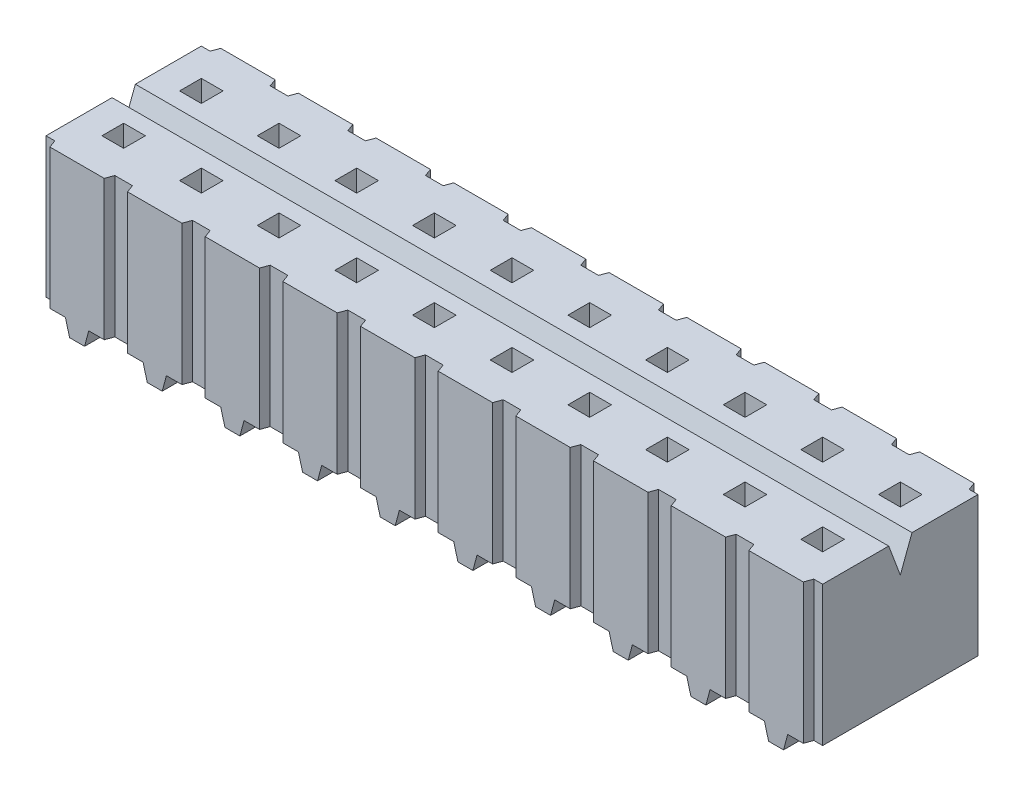
SolidWorks part; units mm, degrees
material "CA"
ref_plane "Front Plane" through (0, 0, 0) normal (0, 0, 1) x (1, 0, 0)
ref_plane "Top Plane" through (0, 0, 0) normal (0, 1, 0) x (1, 0, 0)
ref_plane "Right Plane" through (0, 0, 0) normal (1, 0, 0) x (0, 0, -1)
ref_plane "Plane1" through (0, 0.508, 0) normal (0, -1, 0) x (1, 0, 0)
sketch "Sketch1" plane through (0, 0.508, 0) normal (0, -1, 0) x (1, 0, 0)
  line L0 (-12.319, -2.794) -> (-10.541, -2.794)
  line L1 (-10.541, -2.794) -> (-10.541, -2.54)
  line L2 (-10.541, -2.54) -> (-9.779, -2.54)
  line L3 (-9.779, -2.54) -> (-9.779, -2.794)
  line L4 (-9.779, -2.794) -> (-8.001, -2.794)
  line L5 (-8.001, -2.794) -> (-8.001, -2.54)
  line L6 (-8.001, -2.54) -> (-7.239, -2.54)
  line L7 (-7.239, -2.54) -> (-7.239, -2.794)
  line L8 (-7.239, -2.794) -> (-5.461, -2.794)
  line L9 (-5.461, -2.794) -> (-5.461, -2.54)
  line L10 (-5.461, -2.54) -> (-4.699, -2.54)
  line L11 (-4.699, -2.54) -> (-4.699, -2.794)
  line L12 (-4.699, -2.794) -> (-2.921, -2.794)
  line L13 (-2.921, -2.794) -> (-2.921, -2.54)
  line L14 (-2.921, -2.54) -> (-2.159, -2.54)
  line L15 (-2.159, -2.54) -> (-2.159, -2.794)
  line L16 (-2.159, -2.794) -> (-0.381, -2.794)
  line L17 (-0.381, -2.794) -> (-0.381, -2.54)
  line L18 (-0.381, -2.54) -> (0.381, -2.54)
  line L19 (0.381, -2.54) -> (0.381, -2.794)
  line L20 (0.381, -2.794) -> (2.159, -2.794)
  line L21 (2.159, -2.794) -> (2.159, -2.54)
  line L22 (2.159, -2.54) -> (2.921, -2.54)
  line L23 (2.921, -2.54) -> (2.921, -2.794)
  line L24 (2.921, -2.794) -> (4.699, -2.794)
  line L25 (4.699, -2.794) -> (4.699, -2.54)
  line L26 (4.699, -2.54) -> (5.461, -2.54)
  line L27 (5.461, -2.54) -> (5.461, -2.794)
  line L28 (5.461, -2.794) -> (7.239, -2.794)
  line L29 (7.239, -2.794) -> (7.239, -2.54)
  line L30 (7.239, -2.54) -> (8.001, -2.54)
  line L31 (8.001, -2.54) -> (8.001, -2.794)
  line L32 (8.001, -2.794) -> (9.779, -2.794)
  line L33 (9.779, -2.794) -> (9.779, -2.54)
  line L34 (9.779, -2.54) -> (10.541, -2.54)
  line L35 (10.541, -2.54) -> (10.541, -2.794)
  line L36 (10.541, -2.794) -> (12.319, -2.794)
  line L37 (12.319, -2.794) -> (12.319, -2.54)
  line L38 (12.319, -2.54) -> (12.7, -2.54)
  line L39 (12.7, -2.54) -> (12.7, 2.54)
  line L40 (12.7, 2.54) -> (12.319, 2.54)
  line L41 (12.319, 2.54) -> (12.319, 2.794)
  line L42 (12.319, 2.794) -> (10.541, 2.794)
  line L43 (10.541, 2.794) -> (10.541, 2.54)
  line L44 (10.541, 2.54) -> (9.779, 2.54)
  line L45 (9.779, 2.54) -> (9.779, 2.794)
  line L46 (9.779, 2.794) -> (8.001, 2.794)
  line L47 (8.001, 2.794) -> (8.001, 2.54)
  line L48 (8.001, 2.54) -> (7.239, 2.54)
  line L49 (7.239, 2.54) -> (7.239, 2.794)
  line L50 (7.239, 2.794) -> (5.461, 2.794)
  line L51 (5.461, 2.794) -> (5.461, 2.54)
  line L52 (5.461, 2.54) -> (4.699, 2.54)
  line L53 (4.699, 2.54) -> (4.699, 2.794)
  line L54 (4.699, 2.794) -> (2.921, 2.794)
  line L55 (2.921, 2.794) -> (2.921, 2.54)
  line L56 (2.921, 2.54) -> (2.159, 2.54)
  line L57 (2.159, 2.54) -> (2.159, 2.794)
  line L58 (2.159, 2.794) -> (0.381, 2.794)
  line L59 (0.381, 2.794) -> (0.381, 2.54)
  line L60 (0.381, 2.54) -> (-0.381, 2.54)
  line L61 (-0.381, 2.54) -> (-0.381, 2.794)
  line L62 (-0.381, 2.794) -> (-2.159, 2.794)
  line L63 (-2.159, 2.794) -> (-2.159, 2.54)
  line L64 (-2.159, 2.54) -> (-2.921, 2.54)
  line L65 (-2.921, 2.54) -> (-2.921, 2.794)
  line L66 (-2.921, 2.794) -> (-4.699, 2.794)
  line L67 (-4.699, 2.794) -> (-4.699, 2.54)
  line L68 (-4.699, 2.54) -> (-5.461, 2.54)
  line L69 (-5.461, 2.54) -> (-5.461, 2.794)
  line L70 (-5.461, 2.794) -> (-7.239, 2.794)
  line L71 (-7.239, 2.794) -> (-7.239, 2.54)
  line L72 (-7.239, 2.54) -> (-8.001, 2.54)
  line L73 (-8.001, 2.54) -> (-8.001, 2.794)
  line L74 (-8.001, 2.794) -> (-9.779, 2.794)
  line L75 (-9.779, 2.794) -> (-9.779, 2.54)
  line L76 (-9.779, 2.54) -> (-10.541, 2.54)
  line L77 (-10.541, 2.54) -> (-10.541, 2.794)
  line L78 (-10.541, 2.794) -> (-12.319, 2.794)
  line L79 (-12.319, 2.794) -> (-12.319, 2.54)
  line L80 (-12.319, 2.54) -> (-12.7, 2.54)
  line L81 (-12.7, 2.54) -> (-12.7, -2.54)
  line L82 (-12.7, -2.54) -> (-12.319, -2.54)
  line L83 (-12.319, -2.54) -> (-12.319, -2.794)
extrude "Boss-Extrude1" add sketch "Sketch1" against normal blind 4.572
draft "Draft1" type of draft neutral plane draft angle 20 faces to draft 2 face at (-12.319, 2.794, -2.667) face at (-10.541, 2.794, -2.667) neutral plane through (-12.319, 5.08, -2.794) neutral plane normal (0, 0, -1) parameters "D1"=20
draft "Draft2" type of draft neutral plane draft angle 20 faces to draft 2 face at (-9.779, 2.794, -2.667) face at (-8.001, 2.794, -2.667) neutral plane through (-9.779, 5.08, -2.794) neutral plane normal (0, 0, -1) parameters "D1"=20
draft "Draft3" type of draft neutral plane draft angle 20 faces to draft 2 face at (-7.239, 2.794, -2.667) face at (-5.461, 2.794, -2.667) neutral plane through (-7.239, 5.08, -2.794) neutral plane normal (0, 0, -1) parameters "D1"=20
draft "Draft4" type of draft neutral plane draft angle 20 faces to draft 2 face at (-4.699, 2.794, -2.667) face at (-2.921, 2.794, -2.667) neutral plane through (-4.699, 5.08, -2.794) neutral plane normal (0, 0, -1) parameters "D1"=20
draft "Draft5" type of draft neutral plane draft angle 20 faces to draft 2 face at (-2.159, 2.794, -2.667) face at (-0.381, 2.794, -2.667) neutral plane through (-2.159, 5.08, -2.794) neutral plane normal (0, 0, -1) parameters "D1"=20
draft "Draft6" type of draft neutral plane draft angle 20 faces to draft 2 face at (0.381, 2.794, -2.667) face at (2.159, 2.794, -2.667) neutral plane through (0.381, 5.08, -2.794) neutral plane normal (0, 0, -1) parameters "D1"=20
draft "Draft7" type of draft neutral plane draft angle 20 faces to draft 2 face at (2.921, 2.794, -2.667) face at (4.699, 2.794, -2.667) neutral plane through (2.921, 5.08, -2.794) neutral plane normal (0, 0, -1) parameters "D1"=20
draft "Draft8" type of draft neutral plane draft angle 20 faces to draft 2 face at (5.461, 2.794, -2.667) face at (7.239, 2.794, -2.667) neutral plane through (5.461, 5.08, -2.794) neutral plane normal (0, 0, -1) parameters "D1"=20
draft "Draft9" type of draft neutral plane draft angle 20 faces to draft 2 face at (8.001, 2.794, -2.667) face at (9.779, 2.794, -2.667) neutral plane through (8.001, 5.08, -2.794) neutral plane normal (0, 0, -1) parameters "D1"=20
draft "Draft10" type of draft neutral plane draft angle 20 faces to draft 2 face at (10.541, 2.794, -2.667) face at (12.319, 2.794, -2.667) neutral plane through (10.541, 5.08, -2.794) neutral plane normal (0, 0, -1) parameters "D1"=20
draft "Draft11" type of draft neutral plane draft angle 20 faces to draft 2 face at (-10.541, 2.794, 2.667) face at (-12.319, 2.794, 2.667) neutral plane through (-10.541, 5.08, 2.794) neutral plane normal (0, 0, 1) parameters "D1"=20
draft "Draft12" type of draft neutral plane draft angle 20 faces to draft 2 face at (-8.001, 2.794, 2.667) face at (-9.779, 2.794, 2.667) neutral plane through (-8.001, 5.08, 2.794) neutral plane normal (0, 0, 1) parameters "D1"=20
draft "Draft13" type of draft neutral plane draft angle 20 faces to draft 2 face at (-5.461, 2.794, 2.667) face at (-7.239, 2.794, 2.667) neutral plane through (-5.461, 5.08, 2.794) neutral plane normal (0, 0, 1) parameters "D1"=20
draft "Draft14" type of draft neutral plane draft angle 20 faces to draft 2 face at (-2.921, 2.794, 2.667) face at (-4.699, 2.794, 2.667) neutral plane through (-2.921, 5.08, 2.794) neutral plane normal (0, 0, 1) parameters "D1"=20
draft "Draft15" type of draft neutral plane draft angle 20 faces to draft 2 face at (-0.381, 2.794, 2.667) face at (-2.159, 2.794, 2.667) neutral plane through (-0.381, 5.08, 2.794) neutral plane normal (0, 0, 1) parameters "D1"=20
draft "Draft16" type of draft neutral plane draft angle 20 faces to draft 2 face at (2.159, 2.794, 2.667) face at (0.381, 2.794, 2.667) neutral plane through (2.159, 5.08, 2.794) neutral plane normal (0, 0, 1) parameters "D1"=20
draft "Draft17" type of draft neutral plane draft angle 20 faces to draft 2 face at (4.699, 2.794, 2.667) face at (2.921, 2.794, 2.667) neutral plane through (4.699, 5.08, 2.794) neutral plane normal (0, 0, 1) parameters "D1"=20
draft "Draft18" type of draft neutral plane draft angle 20 faces to draft 2 face at (7.239, 2.794, 2.667) face at (5.461, 2.794, 2.667) neutral plane through (7.239, 5.08, 2.794) neutral plane normal (0, 0, 1) parameters "D1"=20
draft "Draft19" type of draft neutral plane draft angle 20 faces to draft 2 face at (9.779, 2.794, 2.667) face at (8.001, 2.794, 2.667) neutral plane through (9.779, 5.08, 2.794) neutral plane normal (0, 0, 1) parameters "D1"=20
draft "Draft20" type of draft neutral plane draft angle 20 faces to draft 2 face at (10.541, 2.794, 2.667) face at (12.319, 2.794, 2.667) neutral plane through (12.319, 5.08, 2.794) neutral plane normal (0, 0, 1) parameters "D1"=20
sketch "Sketch2" plane through (0, 0.508, 0) normal (0, -1, 0) x (1, 0, 0)
  line L0 (-11.049, -2.794) -> (-11.811, -2.794)
  line L1 (-11.811, -2.794) -> (-11.811, -2.286)
  line L2 (-11.811, -2.286) -> (-11.049, -2.286)
  line L3 (-11.049, -2.286) -> (-11.049, -2.794)
extrude "Boss-Extrude2" add sketch "Sketch2" along normal blind 0.508
sketch "Sketch3" plane through (0, 0.508, 0) normal (0, -1, 0) x (1, 0, 0)
  line L0 (-9.271, -2.286) -> (-8.509, -2.286)
  line L1 (-8.509, -2.286) -> (-8.509, -2.794)
  line L2 (-8.509, -2.794) -> (-9.271, -2.794)
  line L3 (-9.271, -2.794) -> (-9.271, -2.286)
extrude "Boss-Extrude3" add sketch "Sketch3" along normal blind 0.508
sketch "Sketch4" plane through (0, 0.508, 0) normal (0, -1, 0) x (1, 0, 0)
  line L0 (-6.731, -2.286) -> (-5.969, -2.286)
  line L1 (-5.969, -2.286) -> (-5.969, -2.794)
  line L2 (-5.969, -2.794) -> (-6.731, -2.794)
  line L3 (-6.731, -2.794) -> (-6.731, -2.286)
extrude "Boss-Extrude4" add sketch "Sketch4" along normal blind 0.508
sketch "Sketch5" plane through (0, 0.508, 0) normal (0, -1, 0) x (1, 0, 0)
  line L0 (-4.191, -2.286) -> (-3.429, -2.286)
  line L1 (-3.429, -2.286) -> (-3.429, -2.794)
  line L2 (-3.429, -2.794) -> (-4.191, -2.794)
  line L3 (-4.191, -2.794) -> (-4.191, -2.286)
extrude "Boss-Extrude5" add sketch "Sketch5" along normal blind 0.508
sketch "Sketch6" plane through (0, 0.508, 0) normal (0, -1, 0) x (1, 0, 0)
  line L0 (-1.651, -2.286) -> (-0.889, -2.286)
  line L1 (-0.889, -2.286) -> (-0.889, -2.794)
  line L2 (-0.889, -2.794) -> (-1.651, -2.794)
  line L3 (-1.651, -2.794) -> (-1.651, -2.286)
extrude "Boss-Extrude6" add sketch "Sketch6" along normal blind 0.508
sketch "Sketch7" plane through (0, 0.508, 0) normal (0, -1, 0) x (1, 0, 0)
  line L0 (0.889, -2.286) -> (1.651, -2.286)
  line L1 (1.651, -2.286) -> (1.651, -2.794)
  line L2 (1.651, -2.794) -> (0.889, -2.794)
  line L3 (0.889, -2.794) -> (0.889, -2.286)
extrude "Boss-Extrude7" add sketch "Sketch7" along normal blind 0.508
sketch "Sketch8" plane through (0, 0.508, 0) normal (0, -1, 0) x (1, 0, 0)
  line L0 (3.429, -2.286) -> (4.191, -2.286)
  line L1 (4.191, -2.286) -> (4.191, -2.794)
  line L2 (4.191, -2.794) -> (3.429, -2.794)
  line L3 (3.429, -2.794) -> (3.429, -2.286)
extrude "Boss-Extrude8" add sketch "Sketch8" along normal blind 0.508
sketch "Sketch9" plane through (0, 0.508, 0) normal (0, -1, 0) x (1, 0, 0)
  line L0 (5.969, -2.286) -> (6.731, -2.286)
  line L1 (6.731, -2.286) -> (6.731, -2.794)
  line L2 (6.731, -2.794) -> (5.969, -2.794)
  line L3 (5.969, -2.794) -> (5.969, -2.286)
extrude "Boss-Extrude9" add sketch "Sketch9" along normal blind 0.508
sketch "Sketch10" plane through (0, 0.508, 0) normal (0, -1, 0) x (1, 0, 0)
  line L0 (8.509, -2.286) -> (9.271, -2.286)
  line L1 (9.271, -2.286) -> (9.271, -2.794)
  line L2 (9.271, -2.794) -> (8.509, -2.794)
  line L3 (8.509, -2.794) -> (8.509, -2.286)
extrude "Boss-Extrude10" add sketch "Sketch10" along normal blind 0.508
sketch "Sketch11" plane through (0, 0.508, 0) normal (0, -1, 0) x (1, 0, 0)
  line L0 (8.509, 2.794) -> (9.271, 2.794)
  line L1 (9.271, 2.794) -> (9.271, 2.286)
  line L2 (9.271, 2.286) -> (8.509, 2.286)
  line L3 (8.509, 2.286) -> (8.509, 2.794)
extrude "Boss-Extrude11" add sketch "Sketch11" along normal blind 0.508
sketch "Sketch12" plane through (0, 0.508, 0) normal (0, -1, 0) x (1, 0, 0)
  line L0 (5.969, 2.794) -> (6.731, 2.794)
  line L1 (6.731, 2.794) -> (6.731, 2.286)
  line L2 (6.731, 2.286) -> (5.969, 2.286)
  line L3 (5.969, 2.286) -> (5.969, 2.794)
extrude "Boss-Extrude12" add sketch "Sketch12" along normal blind 0.508
sketch "Sketch13" plane through (0, 0.508, 0) normal (0, -1, 0) x (1, 0, 0)
  line L0 (3.429, 2.794) -> (4.191, 2.794)
  line L1 (4.191, 2.794) -> (4.191, 2.286)
  line L2 (4.191, 2.286) -> (3.429, 2.286)
  line L3 (3.429, 2.286) -> (3.429, 2.794)
extrude "Boss-Extrude13" add sketch "Sketch13" along normal blind 0.508
sketch "Sketch14" plane through (0, 0.508, 0) normal (0, -1, 0) x (1, 0, 0)
  line L0 (0.889, 2.794) -> (1.651, 2.794)
  line L1 (1.651, 2.794) -> (1.651, 2.286)
  line L2 (1.651, 2.286) -> (0.889, 2.286)
  line L3 (0.889, 2.286) -> (0.889, 2.794)
extrude "Boss-Extrude14" add sketch "Sketch14" along normal blind 0.508
sketch "Sketch15" plane through (0, 0.508, 0) normal (0, -1, 0) x (1, 0, 0)
  line L0 (-1.651, 2.794) -> (-0.889, 2.794)
  line L1 (-0.889, 2.794) -> (-0.889, 2.286)
  line L2 (-0.889, 2.286) -> (-1.651, 2.286)
  line L3 (-1.651, 2.286) -> (-1.651, 2.794)
extrude "Boss-Extrude15" add sketch "Sketch15" along normal blind 0.508
sketch "Sketch16" plane through (0, 0.508, 0) normal (0, -1, 0) x (1, 0, 0)
  line L0 (-4.191, 2.794) -> (-3.429, 2.794)
  line L1 (-3.429, 2.794) -> (-3.429, 2.286)
  line L2 (-3.429, 2.286) -> (-4.191, 2.286)
  line L3 (-4.191, 2.286) -> (-4.191, 2.794)
extrude "Boss-Extrude16" add sketch "Sketch16" along normal blind 0.508
sketch "Sketch17" plane through (0, 0.508, 0) normal (0, -1, 0) x (1, 0, 0)
  line L0 (-6.731, 2.794) -> (-5.969, 2.794)
  line L1 (-5.969, 2.794) -> (-5.969, 2.286)
  line L2 (-5.969, 2.286) -> (-6.731, 2.286)
  line L3 (-6.731, 2.286) -> (-6.731, 2.794)
extrude "Boss-Extrude17" add sketch "Sketch17" along normal blind 0.508
sketch "Sketch18" plane through (0, 0.508, 0) normal (0, -1, 0) x (1, 0, 0)
  line L0 (-9.271, 2.794) -> (-8.509, 2.794)
  line L1 (-8.509, 2.794) -> (-8.509, 2.286)
  line L2 (-8.509, 2.286) -> (-9.271, 2.286)
  line L3 (-9.271, 2.286) -> (-9.271, 2.794)
extrude "Boss-Extrude18" add sketch "Sketch18" along normal blind 0.508
sketch "Sketch19" plane through (0, 0.508, 0) normal (0, -1, 0) x (1, 0, 0)
  line L0 (-11.049, 2.286) -> (-11.811, 2.286)
  line L1 (-11.811, 2.286) -> (-11.811, 2.794)
  line L2 (-11.811, 2.794) -> (-11.049, 2.794)
  line L3 (-11.049, 2.794) -> (-11.049, 2.286)
extrude "Boss-Extrude19" add sketch "Sketch19" along normal blind 0.508
sketch "Sketch20" plane through (0, 0.508, 0) normal (0, -1, 0) x (1, 0, 0)
  line L0 (11.049, 2.794) -> (11.811, 2.794)
  line L1 (11.811, 2.794) -> (11.811, 2.286)
  line L2 (11.811, 2.286) -> (11.049, 2.286)
  line L3 (11.049, 2.286) -> (11.049, 2.794)
extrude "Boss-Extrude20" add sketch "Sketch20" along normal blind 0.508
sketch "Sketch21" plane through (0, 0.508, 0) normal (0, -1, 0) x (1, 0, 0)
  line L0 (11.049, -2.286) -> (11.811, -2.286)
  line L1 (11.811, -2.286) -> (11.811, -2.794)
  line L2 (11.811, -2.794) -> (11.049, -2.794)
  line L3 (11.049, -2.794) -> (11.049, -2.286)
extrude "Boss-Extrude21" add sketch "Sketch21" along normal blind 0.508
draft "Draft21" type of draft neutral plane draft angle 15 faces to draft 40 face at (-11.049, 0.254, 2.54) face at (-8.509, 0.254, 2.54) face at (-5.969, 0.254, 2.54) face at (-3.429, 0.254, 2.54) face at (-0.889, 0.254, 2.54) face at (1.651, 0.254, 2.54) face at (4.191, 0.254, 2.54) face at (-11.049, 0.254, -2.54) face at (-8.509, 0.254, -2.54) face at (-5.969, 0.254, -2.54) face at (-3.429, 0.254, -2.54) face at (-0.889, 0.254, -2.54) face at (1.651, 0.254, -2.54) face at (4.191, 0.254, -2.54) face at (6.731, 0.254, 2.54) face at (6.731, 0.254, -2.54) face at (9.271, 0.254, 2.54) face at (9.271, 0.254, -2.54) face at (11.811, 0.254, 2.54) face at (11.811, 0.254, -2.54) face at (-9.271, 0.254, 2.54) face at (-6.731, 0.254, 2.54) face at (-4.191, 0.254, 2.54) face at (-1.651, 0.254, 2.54) face at (0.889, 0.254, 2.54) face at (3.429, 0.254, 2.54) face at (5.969, 0.254, 2.54) face at (8.509, 0.254, 2.54) face at (11.049, 0.254, 2.54) face at (11.049, 0.254, -2.54) face at (8.509, 0.254, -2.54) face at (5.969, 0.254, -2.54) face at (3.429, 0.254, -2.54) face at (0.889, 0.254, -2.54) face at (-1.651, 0.254, -2.54) face at (-4.191, 0.254, -2.54) face at (-6.731, 0.254, -2.54) face at (-9.271, 0.254, -2.54) face at (-11.811, 0.254, -2.54) face at (-11.811, 0.254, 2.54) neutral plane through (0, 0.508, 0) neutral plane normal (0, -1, 0) parameters "D1"=15
sketch "Sketch22" plane through (12.7, 0, 0) normal (1, 0, 0) x (0, 0, -1)
  line L0 (0.381, 5.08) -> (-0.381, 5.08)
  line L1 (-0.381, 5.08) -> (0, 4.064)
  line L2 (0, 4.064) -> (0.381, 5.08)
extrude "Cut-Extrude1" cut sketch "Sketch22" against normal through all
sketch "Sketch23" plane through (0, 5.08, 0) normal (0, 1, 0) x (-1, 0, 0)
  line L0 (5.9944, 0.9144) -> (6.7056, 0.9144)
  line L1 (6.7056, 0.9144) -> (6.7056, 1.6256)
  line L2 (6.7056, 1.6256) -> (5.9944, 1.6256)
  line L3 (5.9944, 1.6256) -> (5.9944, 0.9144)
extrude "Cut-Extrude2" cut sketch "Sketch23" against normal blind 4.318
sketch "Sketch24" plane through (0, 5.08, 0) normal (0, 1, 0) x (-1, 0, 0)
  line L0 (3.4544, 0.9144) -> (4.1656, 0.9144)
  line L1 (4.1656, 0.9144) -> (4.1656, 1.6256)
  line L2 (4.1656, 1.6256) -> (3.4544, 1.6256)
  line L3 (3.4544, 1.6256) -> (3.4544, 0.9144)
extrude "Cut-Extrude3" cut sketch "Sketch24" against normal blind 4.318
sketch "Sketch25" plane through (0, 5.08, 0) normal (0, 1, 0) x (-1, 0, 0)
  line L0 (0.9144, 0.9144) -> (1.6256, 0.9144)
  line L1 (1.6256, 0.9144) -> (1.6256, 1.6256)
  line L2 (1.6256, 1.6256) -> (0.9144, 1.6256)
  line L3 (0.9144, 1.6256) -> (0.9144, 0.9144)
extrude "Cut-Extrude4" cut sketch "Sketch25" against normal blind 4.318
sketch "Sketch26" plane through (0, 5.08, 0) normal (0, 1, 0) x (-1, 0, 0)
  line L0 (-1.6256, 0.9144) -> (-0.9144, 0.9144)
  line L1 (-0.9144, 0.9144) -> (-0.9144, 1.6256)
  line L2 (-0.9144, 1.6256) -> (-1.6256, 1.6256)
  line L3 (-1.6256, 1.6256) -> (-1.6256, 0.9144)
extrude "Cut-Extrude5" cut sketch "Sketch26" against normal blind 4.318
sketch "Sketch27" plane through (0, 5.08, 0) normal (0, 1, 0) x (-1, 0, 0)
  line L0 (-4.1656, 0.9144) -> (-3.4544, 0.9144)
  line L1 (-3.4544, 0.9144) -> (-3.4544, 1.6256)
  line L2 (-3.4544, 1.6256) -> (-4.1656, 1.6256)
  line L3 (-4.1656, 1.6256) -> (-4.1656, 0.9144)
extrude "Cut-Extrude6" cut sketch "Sketch27" against normal blind 4.318
sketch "Sketch28" plane through (0, 5.08, 0) normal (0, 1, 0) x (-1, 0, 0)
  line L0 (-6.7056, 0.9144) -> (-5.9944, 0.9144)
  line L1 (-5.9944, 0.9144) -> (-5.9944, 1.6256)
  line L2 (-5.9944, 1.6256) -> (-6.7056, 1.6256)
  line L3 (-6.7056, 1.6256) -> (-6.7056, 0.9144)
extrude "Cut-Extrude7" cut sketch "Sketch28" against normal blind 4.318
sketch "Sketch29" plane through (0, 5.08, 0) normal (0, 1, 0) x (-1, 0, 0)
  line L0 (-9.2456, 0.9144) -> (-8.5344, 0.9144)
  line L1 (-8.5344, 0.9144) -> (-8.5344, 1.6256)
  line L2 (-8.5344, 1.6256) -> (-9.2456, 1.6256)
  line L3 (-9.2456, 1.6256) -> (-9.2456, 0.9144)
extrude "Cut-Extrude8" cut sketch "Sketch29" against normal blind 4.318
sketch "Sketch30" plane through (0, 5.08, 0) normal (0, 1, 0) x (-1, 0, 0)
  line L0 (-11.7856, 0.9144) -> (-11.0744, 0.9144)
  line L1 (-11.0744, 0.9144) -> (-11.0744, 1.6256)
  line L2 (-11.0744, 1.6256) -> (-11.7856, 1.6256)
  line L3 (-11.7856, 1.6256) -> (-11.7856, 0.9144)
extrude "Cut-Extrude9" cut sketch "Sketch30" against normal blind 4.318
sketch "Sketch31" plane through (0, 5.08, 0) normal (0, 1, 0) x (-1, 0, 0)
  line L0 (8.5344, 0.9144) -> (9.2456, 0.9144)
  line L1 (9.2456, 0.9144) -> (9.2456, 1.6256)
  line L2 (9.2456, 1.6256) -> (8.5344, 1.6256)
  line L3 (8.5344, 1.6256) -> (8.5344, 0.9144)
extrude "Cut-Extrude10" cut sketch "Sketch31" against normal blind 4.318
sketch "Sketch32" plane through (0, 5.08, 0) normal (0, 1, 0) x (-1, 0, 0)
  line L0 (11.0744, 0.9144) -> (11.7856, 0.9144)
  line L1 (11.7856, 0.9144) -> (11.7856, 1.6256)
  line L2 (11.7856, 1.6256) -> (11.0744, 1.6256)
  line L3 (11.0744, 1.6256) -> (11.0744, 0.9144)
extrude "Cut-Extrude11" cut sketch "Sketch32" against normal blind 4.318
sketch "Sketch33" plane through (0, 5.08, 0) normal (0, 1, 0) x (-1, 0, 0)
  line L0 (-11.7856, -1.6256) -> (-11.0744, -1.6256)
  line L1 (-11.0744, -1.6256) -> (-11.0744, -0.9144)
  line L2 (-11.0744, -0.9144) -> (-11.7856, -0.9144)
  line L3 (-11.7856, -0.9144) -> (-11.7856, -1.6256)
extrude "Cut-Extrude12" cut sketch "Sketch33" against normal blind 4.318
sketch "Sketch34" plane through (0, 5.08, 0) normal (0, 1, 0) x (-1, 0, 0)
  line L0 (-9.2456, -1.6256) -> (-8.5344, -1.6256)
  line L1 (-8.5344, -1.6256) -> (-8.5344, -0.9144)
  line L2 (-8.5344, -0.9144) -> (-9.2456, -0.9144)
  line L3 (-9.2456, -0.9144) -> (-9.2456, -1.6256)
extrude "Cut-Extrude13" cut sketch "Sketch34" against normal blind 4.318
sketch "Sketch35" plane through (0, 5.08, 0) normal (0, 1, 0) x (-1, 0, 0)
  line L0 (-6.7056, -1.6256) -> (-5.9944, -1.6256)
  line L1 (-5.9944, -1.6256) -> (-5.9944, -0.9144)
  line L2 (-5.9944, -0.9144) -> (-6.7056, -0.9144)
  line L3 (-6.7056, -0.9144) -> (-6.7056, -1.6256)
extrude "Cut-Extrude14" cut sketch "Sketch35" against normal blind 4.318
sketch "Sketch36" plane through (0, 5.08, 0) normal (0, 1, 0) x (-1, 0, 0)
  line L0 (-4.1656, -1.6256) -> (-3.4544, -1.6256)
  line L1 (-3.4544, -1.6256) -> (-3.4544, -0.9144)
  line L2 (-3.4544, -0.9144) -> (-4.1656, -0.9144)
  line L3 (-4.1656, -0.9144) -> (-4.1656, -1.6256)
extrude "Cut-Extrude15" cut sketch "Sketch36" against normal blind 4.318
sketch "Sketch37" plane through (0, 5.08, 0) normal (0, 1, 0) x (-1, 0, 0)
  line L0 (-1.6256, -1.6256) -> (-0.9144, -1.6256)
  line L1 (-0.9144, -1.6256) -> (-0.9144, -0.9144)
  line L2 (-0.9144, -0.9144) -> (-1.6256, -0.9144)
  line L3 (-1.6256, -0.9144) -> (-1.6256, -1.6256)
extrude "Cut-Extrude16" cut sketch "Sketch37" against normal blind 4.318
sketch "Sketch38" plane through (0, 5.08, 0) normal (0, 1, 0) x (-1, 0, 0)
  line L0 (0.9144, -1.6256) -> (1.6256, -1.6256)
  line L1 (1.6256, -1.6256) -> (1.6256, -0.9144)
  line L2 (1.6256, -0.9144) -> (0.9144, -0.9144)
  line L3 (0.9144, -0.9144) -> (0.9144, -1.6256)
extrude "Cut-Extrude17" cut sketch "Sketch38" against normal blind 4.318
sketch "Sketch39" plane through (0, 5.08, 0) normal (0, 1, 0) x (-1, 0, 0)
  line L0 (3.4544, -1.6256) -> (4.1656, -1.6256)
  line L1 (4.1656, -1.6256) -> (4.1656, -0.9144)
  line L2 (4.1656, -0.9144) -> (3.4544, -0.9144)
  line L3 (3.4544, -0.9144) -> (3.4544, -1.6256)
extrude "Cut-Extrude18" cut sketch "Sketch39" against normal blind 4.318
sketch "Sketch40" plane through (0, 5.08, 0) normal (0, 1, 0) x (-1, 0, 0)
  line L0 (5.9944, -1.6256) -> (6.7056, -1.6256)
  line L1 (6.7056, -1.6256) -> (6.7056, -0.9144)
  line L2 (6.7056, -0.9144) -> (5.9944, -0.9144)
  line L3 (5.9944, -0.9144) -> (5.9944, -1.6256)
extrude "Cut-Extrude19" cut sketch "Sketch40" against normal blind 4.318
sketch "Sketch41" plane through (0, 5.08, 0) normal (0, 1, 0) x (-1, 0, 0)
  line L0 (8.5344, -1.6256) -> (9.2456, -1.6256)
  line L1 (9.2456, -1.6256) -> (9.2456, -0.9144)
  line L2 (9.2456, -0.9144) -> (8.5344, -0.9144)
  line L3 (8.5344, -0.9144) -> (8.5344, -1.6256)
extrude "Cut-Extrude20" cut sketch "Sketch41" against normal blind 4.318
sketch "Sketch42" plane through (0, 5.08, 0) normal (0, 1, 0) x (-1, 0, 0)
  line L0 (11.0744, -1.6256) -> (11.7856, -1.6256)
  line L1 (11.7856, -1.6256) -> (11.7856, -0.9144)
  line L2 (11.7856, -0.9144) -> (11.0744, -0.9144)
  line L3 (11.0744, -0.9144) -> (11.0744, -1.6256)
extrude "Cut-Extrude21" cut sketch "Sketch42" against normal blind 4.318
